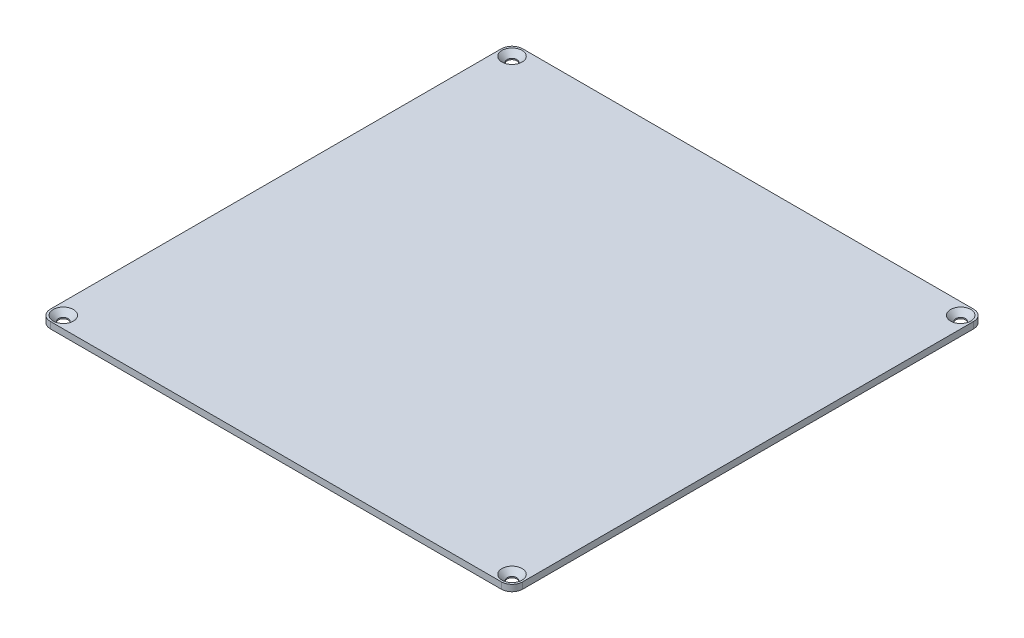
SolidWorks part; units mm, degrees
material "1060 Alloy"
ref_plane "Front Plane" through (0, 0, 0) normal (0, 0, 1) x (1, 0, 0)
ref_plane "Top Plane" through (0, 0, 0) normal (0, 1, 0) x (1, 0, 0)
ref_plane "Right Plane" through (0, 0, 0) normal (1, 0, 0) x (0, 0, -1)
sketch "Sketch1" plane through (0, 0, 0) normal (0, 1, 0) x (1, 0, 0)
  line L1 (-110, -110) -> (110, -110)
  line L2 (-110, -110) -> (-110, 110)
  line L3 (-110, 110) -> (110, 110)
  line L4 (110, -110) -> (110, 110)
  line L5 (-110, -110) -> (110, 110) construction
  line L6 (-110, 110) -> (110, -110) construction
  point P0 (0, 0)
  dimension "D1" = 220
extrude "Boss-Extrude1" add sketch "Sketch1" along normal blind 3
fillet "Fillet1" radius 5 4 edges at (110, 1.5, -110) (-110, 1.5, -110) (-110, 1.5, 110) (110, 1.5, 110)
sketch "Sketch3" plane through (0, 3, 0) normal (0, 1, 0) x (1, 0, 0)
  line L0 (-128.0985, 0) -> (134.2825, 0) construction
  line L1 (0, 119.853) -> (0, -119.853) construction
  circle A0 centre (-104.5, 104.5) radius 2
  circle A1 centre (104.5, 104.5) radius 2
  circle A2 centre (-104.5, -104.5) radius 2
  circle A3 centre (104.5, -104.5) radius 2
  point P0 (-104.5, 104.5)
  point P2 (104.5, 104.5)
  point P4 (-104.5, -104.5)
  point P6 (104.5, -104.5)
  dimension "D1" = 4
  dimension "D2" = 209
  dimension "D3" = 209
hole_wizard "CSK for M4 Countersunk Flat Head Screw1" positions "Sketch3" profile "Sketch4" countersink size "M4" standard "ISO" end condition through all
sketch "Sketch4" plane through (-104.5, 3, -104.5) normal (1, 0, 0) x (0, 0, 1)
  line L0 (0, 0) -> (0, 3)
  line L1 (0, 3) -> (2.25, 3)
  line L2 (2.25, 3) -> (2.25, 2.45)
  line L3 (2.25, 2.45) -> (4.7, 0)
  line L5 (4.7, 0) -> (0, 0)
  line L6 (-2.25, 2.45) -> (-4.7, 0) construction
  line L11 (0, -6.35) -> (0, 107.95) construction
  dimension "Thru Hole Dia." = 4.5
  dimension "Thru Hole Depth" = 3
  dimension "Near C'Sink Dia." = 9.4
  dimension "Near C'Sink Angle" = 90
